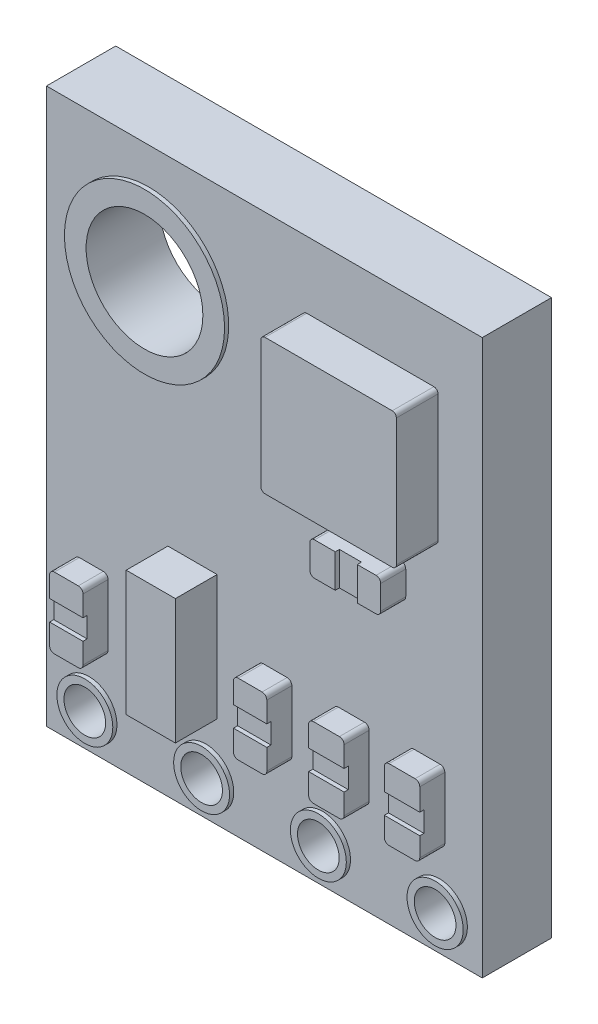
SolidWorks part; units mm, degrees
ref_plane "Alzado" through (0, 0, 0) normal (0, 0, 1) x (1, 0, 0)
ref_plane "Planta" through (0, 0, 0) normal (0, 1, 0) x (1, 0, 0)
ref_plane "Vista lateral" through (0, 0, 0) normal (1, 0, 0) x (0, 0, -1)
sketch "Croquis1" plane through (0, 0, 0) normal (0, 0, 1) x (1, 0, 0)
  line L0 (-5.225, 6.65) -> (5.225, 6.65)
  line L1 (5.225, 6.65) -> (5.225, -6.65)
  line L2 (5.225, -6.65) -> (-5.225, -6.65)
  line L3 (-5.225, -6.65) -> (-5.225, 6.65)
  line L4 (-2.775, 5.26) -> (-2.775, 2.46) construction
  line L5 (-4.175, 3.86) -> (-2.5214, 3.86) construction
  circle A0 centre (-2.775, 3.86) radius 1.4
  point P3 (-5.225, 0)
  point P5 (0, -6.65)
  dimension "D5" = 2.8
  dimension "D1" = 13.3
  dimension "D2" = 10.45
  dimension "D3" = 1.05
  dimension "D4" = 1.39
extrude "Saliente-Extruir1" add sketch "Croquis1" along normal blind 1.66
sketch "Croquis2" plane through (0, 0, 1.66) normal (0, 0, 1) x (1, 0, 0)
  line L0 (1.0149, 5.05) -> (4.0649, 5.05)
  line L1 (4.1649, 4.95) -> (4.1649, 1.9)
  line L2 (4.0649, 1.8) -> (1.0149, 1.8)
  line L3 (0.9149, 1.9) -> (0.9149, 4.95)
  line L4 (5.225, 6.65) -> (-5.225, 6.65) construction
  line L5 (1.8027, 1.0381) -> (3.277, 1.0381) construction
  line L6 (3.3899, 0.9253) -> (3.3899, 0.351) construction
  line L7 (3.277, 0.2381) -> (1.8027, 0.2381) construction
  line L8 (1.6899, 0.351) -> (1.6899, 0.9253) construction
  line L9 (-4.437, -2.75) -> (-3.8627, -2.75) construction
  line L10 (-3.7498, -2.8628) -> (-3.7498, -4.3372) construction
  line L11 (-3.8627, -4.45) -> (-4.437, -4.45) construction
  line L12 (-4.5498, -4.3372) -> (-4.5498, -2.8628) construction
  line L13 (-2.3141, -1.45) -> (-1.1341, -1.45) construction
  line L14 (-1.1341, -1.45) -> (-1.1341, -4.45) construction
  line L15 (-1.1341, -4.45) -> (-2.3141, -4.45) construction
  line L16 (-2.3141, -4.45) -> (-2.3141, -1.45) construction
  line L17 (-0.0292, -2.75) -> (0.5451, -2.75) construction
  line L18 (0.6579, -2.8628) -> (0.6579, -4.3372) construction
  line L19 (0.5451, -4.45) -> (-0.0292, -4.45) construction
  line L20 (-0.1421, -4.3372) -> (-0.1421, -2.8628) construction
  line L21 (1.774, -2.75) -> (2.3983, -2.75) construction
  line L22 (2.5112, -2.8628) -> (2.5112, -4.3372) construction
  line L23 (2.3983, -4.45) -> (1.774, -4.45) construction
  line L24 (1.6612, -4.3372) -> (1.6612, -2.8628) construction
  line L26 (3.589, -2.7167) -> (4.2133, -2.7167) construction
  line L27 (4.3261, -2.8296) -> (4.3261, -4.3039) construction
  line L28 (4.2133, -4.4167) -> (3.589, -4.4167) construction
  line L29 (3.4761, -4.3039) -> (3.4761, -2.8296) construction
  arc A0 (1.0149, 1.8) -> (0.9149, 1.9) centre (1.0149, 1.9) cw
  arc A1 (4.1649, 1.9) -> (4.0649, 1.8) centre (4.0649, 1.9) cw
  arc A2 (4.0649, 5.05) -> (4.1649, 4.95) centre (4.0649, 4.95) cw
  arc A3 (1.0149, 5.05) -> (0.9149, 4.95) centre (1.0149, 4.95) ccw
  arc A4 (4.3261, -4.3039) -> (4.2133, -4.4167) centre (4.2133, -4.3039) cw construction
  arc A5 (3.589, -4.4167) -> (3.4761, -4.3039) centre (3.589, -4.3039) cw construction
  arc A6 (4.2133, -2.7167) -> (4.3261, -2.8296) centre (4.2133, -2.8296) cw construction
  arc A7 (3.4761, -2.8296) -> (3.589, -2.7167) centre (3.589, -2.8296) cw construction
  arc A8 (2.3983, -2.75) -> (2.5112, -2.8628) centre (2.3983, -2.8628) cw construction
  arc A9 (2.5112, -4.3372) -> (2.3983, -4.45) centre (2.3983, -4.3372) cw construction
  arc A10 (1.774, -4.45) -> (1.6612, -4.3372) centre (1.774, -4.3372) cw construction
  arc A11 (1.774, -2.75) -> (1.6612, -2.8628) centre (1.774, -2.8628) ccw construction
  arc A12 (0.5451, -2.75) -> (0.6579, -2.8628) centre (0.5451, -2.8628) cw construction
  arc A13 (0.6579, -4.3372) -> (0.5451, -4.45) centre (0.5451, -4.3372) cw construction
  arc A14 (-0.0292, -4.45) -> (-0.1421, -4.3372) centre (-0.0292, -4.3372) cw construction
  arc A15 (-0.0292, -2.75) -> (-0.1421, -2.8628) centre (-0.0292, -2.8628) ccw construction
  arc A16 (3.277, 1.0381) -> (3.3899, 0.9253) centre (3.277, 0.9253) cw construction
  arc A17 (3.3899, 0.351) -> (3.277, 0.2381) centre (3.277, 0.351) cw construction
  arc A18 (1.8027, 0.2381) -> (1.6899, 0.351) centre (1.8027, 0.351) cw construction
  arc A19 (1.8027, 1.0381) -> (1.6899, 0.9253) centre (1.8027, 0.9253) ccw construction
  arc A20 (-4.437, -4.45) -> (-4.5498, -4.3372) centre (-4.437, -4.3372) cw construction
  arc A21 (-3.7498, -4.3372) -> (-3.8627, -4.45) centre (-3.8627, -4.3372) cw construction
  arc A22 (-3.8627, -2.75) -> (-3.7498, -2.8628) centre (-3.8627, -2.8628) cw construction
  arc A23 (-4.437, -2.75) -> (-4.5498, -2.8628) centre (-4.437, -2.8628) ccw construction
  circle A24 centre (-4.2058, -5.774) radius 0.5 construction
  circle A25 centre (-1.4058, -5.774) radius 0.5 construction
  circle A26 centre (1.3942, -5.774) radius 0.5 construction
  circle A27 centre (4.1942, -5.774) radius 0.5 construction
  point P10 (4.1649, 1.8)
  point P13 (4.1649, 5.05)
  point P36 (2.5399, 1.0381)
  point P38 (2.5399, 1.8)
  point P44 (4.3261, -4.4167)
  point P49 (4.3261, -2.7167)
  point P56 (2.5112, -4.45)
  point P59 (1.6612, -4.45)
  point P64 (0.6579, -2.75)
  point P75 (3.3899, 0.2381)
  point P78 (1.6899, 0.2381)
  point P81 (1.6899, 1.0381)
  point P84 (-4.5498, -4.45)
  point P87 (-3.7498, -4.45)
  point P90 (-3.7498, -2.75)
  point P93 (-4.5498, -2.75)
  dimension "D3" = 0.1
  dimension "D12" = 0.1128
  dimension "D14" = 1
  dimension "D1" = 3.25
  dimension "D2" = 4.85
  dimension "D4" = 3
  dimension "D5" = 1.18
  dimension "D6" = 1.7
  dimension "D7" = 0.8
  dimension "D8" = 0.85
  dimension "D9" = 1.7
  dimension "D10" = 0.8
  dimension "D11" = 1.7
  dimension "D13" = 4
extrude "Saliente-Extruir2" add sketch "Croquis2" along normal blind 1
sketch "Croquis3" plane through (0, 0, 1.66) normal (0, 0, 1) x (1, 0, 0)
  line L0 (0.5451, -4.45) -> (-0.0292, -4.45) construction
  line L1 (-4.437, -2.75) -> (-3.8627, -2.75) construction
  line L2 (-3.7498, -2.8628) -> (-3.7498, -4.3372) construction
  line L3 (-3.8627, -4.45) -> (-4.437, -4.45) construction
  line L4 (-4.5498, -4.3372) -> (-4.5498, -2.8628) construction
  line L5 (0.6579, -2.8628) -> (0.6579, -4.3372) construction
  line L6 (-0.1421, -4.3372) -> (-0.1421, -2.8628) construction
  line L7 (-0.0292, -2.75) -> (0.5451, -2.75) construction
  line L8 (0.5451, -4.45) -> (-0.0292, -4.45)
  line L9 (-0.0292, -2.75) -> (0.5451, -2.75)
  line L10 (-0.1421, -4.3372) -> (-0.1421, -2.8628)
  line L11 (0.6579, -2.8628) -> (0.6579, -4.3372)
  line L12 (-4.5498, -4.3372) -> (-4.5498, -2.8628)
  line L13 (-3.8627, -4.45) -> (-4.437, -4.45)
  line L14 (-3.7498, -2.8628) -> (-3.7498, -4.3372)
  line L15 (-4.437, -2.75) -> (-3.8627, -2.75)
  line L16 (3.589, -2.7167) -> (4.2133, -2.7167) construction
  line L17 (4.3261, -2.8296) -> (4.3261, -4.3039) construction
  line L18 (3.4761, -4.3039) -> (3.4761, -2.8296) construction
  line L19 (4.2133, -4.4167) -> (3.589, -4.4167) construction
  line L20 (1.6612, -4.3372) -> (1.6612, -2.8628) construction
  line L21 (1.774, -2.75) -> (2.3983, -2.75) construction
  line L22 (2.5112, -2.8628) -> (2.5112, -4.3372) construction
  line L23 (2.3983, -4.45) -> (1.774, -4.45) construction
  line L24 (3.589, -2.7167) -> (4.2133, -2.7167)
  line L25 (4.3261, -2.8296) -> (4.3261, -4.3039)
  line L26 (3.4761, -4.3039) -> (3.4761, -2.8296)
  line L27 (4.2133, -4.4167) -> (3.589, -4.4167)
  line L28 (1.6612, -4.3372) -> (1.6612, -2.8628)
  line L29 (1.774, -2.75) -> (2.3983, -2.75)
  line L30 (2.5112, -2.8628) -> (2.5112, -4.3372)
  line L31 (2.3983, -4.45) -> (1.774, -4.45)
  line L32 (1.6899, 0.351) -> (1.6899, 0.9253) construction
  line L33 (1.8027, 1.0381) -> (3.277, 1.0381) construction
  line L34 (3.3899, 0.9253) -> (3.3899, 0.351) construction
  line L35 (3.277, 0.2381) -> (1.8027, 0.2381) construction
  line L36 (1.6899, 0.351) -> (1.6899, 0.9253)
  line L37 (1.8027, 1.0381) -> (3.277, 1.0381)
  line L38 (3.3899, 0.9253) -> (3.3899, 0.351)
  line L39 (3.277, 0.2381) -> (1.8027, 0.2381)
  arc A0 (-3.7498, -2.8628) -> (-3.8627, -2.75) centre (-3.8627, -2.8628) ccw construction
  arc A1 (-3.8627, -4.45) -> (-3.7498, -4.3372) centre (-3.8627, -4.3372) ccw construction
  arc A2 (-4.5498, -4.3372) -> (-4.437, -4.45) centre (-4.437, -4.3372) ccw construction
  arc A3 (-4.437, -2.75) -> (-4.5498, -2.8628) centre (-4.437, -2.8628) ccw construction
  arc A4 (-0.1421, -4.3372) -> (-0.0292, -4.45) centre (-0.0292, -4.3372) ccw construction
  arc A5 (0.6579, -2.8628) -> (0.5451, -2.75) centre (0.5451, -2.8628) ccw construction
  arc A6 (-0.0292, -2.75) -> (-0.1421, -2.8628) centre (-0.0292, -2.8628) ccw construction
  arc A7 (0.5451, -4.45) -> (0.6579, -4.3372) centre (0.5451, -4.3372) ccw construction
  arc A8 (0.5451, -4.45) -> (0.6579, -4.3372) centre (0.5451, -4.3372) ccw
  arc A9 (-0.0292, -2.75) -> (-0.1421, -2.8628) centre (-0.0292, -2.8628) ccw
  arc A10 (0.6579, -2.8628) -> (0.5451, -2.75) centre (0.5451, -2.8628) ccw
  arc A11 (-0.1421, -4.3372) -> (-0.0292, -4.45) centre (-0.0292, -4.3372) ccw
  arc A12 (-4.437, -2.75) -> (-4.5498, -2.8628) centre (-4.437, -2.8628) ccw
  arc A13 (-4.5498, -4.3372) -> (-4.437, -4.45) centre (-4.437, -4.3372) ccw
  arc A14 (-3.8627, -4.45) -> (-3.7498, -4.3372) centre (-3.8627, -4.3372) ccw
  arc A15 (-3.7498, -2.8628) -> (-3.8627, -2.75) centre (-3.8627, -2.8628) ccw
  arc A16 (3.589, -2.7167) -> (3.4761, -2.8296) centre (3.589, -2.8296) ccw construction
  arc A17 (4.3261, -2.8296) -> (4.2133, -2.7167) centre (4.2133, -2.8296) ccw construction
  arc A18 (4.2133, -4.4167) -> (4.3261, -4.3039) centre (4.2133, -4.3039) ccw construction
  arc A19 (3.4761, -4.3039) -> (3.589, -4.4167) centre (3.589, -4.3039) ccw construction
  arc A20 (1.6612, -4.3372) -> (1.774, -4.45) centre (1.774, -4.3372) ccw construction
  arc A21 (1.774, -2.75) -> (1.6612, -2.8628) centre (1.774, -2.8628) ccw construction
  arc A22 (2.5112, -2.8628) -> (2.3983, -2.75) centre (2.3983, -2.8628) ccw construction
  arc A23 (2.3983, -4.45) -> (2.5112, -4.3372) centre (2.3983, -4.3372) ccw construction
  arc A24 (3.589, -2.7167) -> (3.4761, -2.8296) centre (3.589, -2.8296) ccw
  arc A25 (4.3261, -2.8296) -> (4.2133, -2.7167) centre (4.2133, -2.8296) ccw
  arc A26 (4.2133, -4.4167) -> (4.3261, -4.3039) centre (4.2133, -4.3039) ccw
  arc A27 (3.4761, -4.3039) -> (3.589, -4.4167) centre (3.589, -4.3039) ccw
  arc A28 (1.6612, -4.3372) -> (1.774, -4.45) centre (1.774, -4.3372) ccw
  arc A29 (1.774, -2.75) -> (1.6612, -2.8628) centre (1.774, -2.8628) ccw
  arc A30 (2.5112, -2.8628) -> (2.3983, -2.75) centre (2.3983, -2.8628) ccw
  arc A31 (2.3983, -4.45) -> (2.5112, -4.3372) centre (2.3983, -4.3372) ccw
  arc A32 (1.6899, 0.351) -> (1.8027, 0.2381) centre (1.8027, 0.351) ccw construction
  arc A33 (1.8027, 1.0381) -> (1.6899, 0.9253) centre (1.8027, 0.9253) ccw construction
  arc A34 (3.3899, 0.9253) -> (3.277, 1.0381) centre (3.277, 0.9253) ccw construction
  arc A35 (3.277, 0.2381) -> (3.3899, 0.351) centre (3.277, 0.351) ccw construction
  arc A36 (1.6899, 0.351) -> (1.8027, 0.2381) centre (1.8027, 0.351) ccw
  arc A37 (1.8027, 1.0381) -> (1.6899, 0.9253) centre (1.8027, 0.9253) ccw
  arc A38 (3.3899, 0.9253) -> (3.277, 1.0381) centre (3.277, 0.9253) ccw
  arc A39 (3.277, 0.2381) -> (3.3899, 0.351) centre (3.277, 0.351) ccw
extrude "Saliente-Extruir3" add sketch "Croquis3" along normal blind 0.6
sketch "Croquis4" plane through (0, 0, 1.66) normal (0, 0, 1) x (1, 0, 0)
  circle A0 centre (4.1942, -5.774) radius 0.5 construction
  circle A1 centre (1.3942, -5.774) radius 0.5 construction
  circle A2 centre (-1.4058, -5.774) radius 0.5 construction
  circle A3 centre (-4.2058, -5.774) radius 0.5 construction
  circle A4 centre (4.1942, -5.774) radius 0.5
  circle A5 centre (1.3942, -5.774) radius 0.5
  circle A6 centre (-1.4058, -5.774) radius 0.5
  circle A7 centre (-4.2058, -5.774) radius 0.5
extrude "Cortar-Extruir1" cut sketch "Croquis4" against normal blind 2
sketch "Croquis5" plane through (0, 0, 1.66) normal (0, 0, 1) x (1, 0, 0)
  line L0 (-2.3141, -1.45) -> (-1.1341, -1.45) construction
  line L1 (-2.3141, -4.45) -> (-2.3141, -1.45) construction
  line L2 (-1.1341, -1.45) -> (-1.1341, -4.45) construction
  line L3 (-1.1341, -4.45) -> (-2.3141, -4.45) construction
  line L4 (-2.3141, -1.45) -> (-1.1341, -1.45)
  line L5 (-2.3141, -4.45) -> (-2.3141, -1.45)
  line L6 (-1.1341, -1.45) -> (-1.1341, -4.45)
  line L7 (-1.1341, -4.45) -> (-2.3141, -4.45)
extrude "Saliente-Extruir4" add sketch "Croquis5" along normal blind 1
sketch "Croquis6" plane through (0, 0, 1.66) normal (0, 0, 1) x (1, 0, 0)
  circle A0 centre (-4.2058, -5.774) radius 0.6705
  circle A1 centre (-1.4058, -5.774) radius 0.6705
  circle A2 centre (1.3942, -5.774) radius 0.6705
  circle A3 centre (4.1942, -5.774) radius 0.6732
  circle A4 centre (-2.775, 3.86) radius 1.9201
  circle A5 centre (4.1942, -5.774) radius 0.5 construction
  circle A6 centre (1.3942, -5.774) radius 0.5 construction
  circle A7 centre (-1.4058, -5.774) radius 0.5 construction
  circle A8 centre (-4.2058, -5.774) radius 0.5 construction
  circle A9 centre (-2.775, 3.86) radius 1.4 construction
  circle A10 centre (4.1942, -5.774) radius 0.5
  circle A11 centre (1.3942, -5.774) radius 0.5
  circle A12 centre (-1.4058, -5.774) radius 0.5
  circle A13 centre (-4.2058, -5.774) radius 0.5
  circle A14 centre (-2.775, 3.86) radius 1.4
extrude "Saliente-Extruir5" add sketch "Croquis6" along normal blind 0.1
sketch "Croquis7" plane through (0, 0, 2.26) normal (0, 0, 1) x (1, 0, 0)
  line L2 (-4.5498, -3.845) -> (-3.7498, -3.845)
  line L3 (-4.5498, -4.3372) -> (-4.5498, -2.8628) construction
  line L4 (-3.7498, -2.8628) -> (-3.7498, -4.3372) construction
  line L5 (-3.7498, -3.845) -> (-3.7498, -3.3567)
  line L6 (-3.7498, -3.3567) -> (-4.5498, -3.3567)
  line L7 (-4.5498, -3.3567) -> (-4.5498, -3.845)
  line L8 (-0.1421, -3.845) -> (0.6579, -3.845)
  line L9 (-0.1421, -4.3372) -> (-0.1421, -2.8628) construction
  line L10 (0.6579, -2.8628) -> (0.6579, -4.3372) construction
  line L11 (0.6579, -3.845) -> (0.6579, -3.3567)
  line L12 (0.6579, -3.3567) -> (-0.1421, -3.3567)
  line L13 (-0.1421, -3.3567) -> (-0.1421, -3.845)
  line L14 (1.6612, -3.3567) -> (2.5112, -3.3567)
  line L15 (1.6612, -4.3372) -> (1.6612, -2.8628) construction
  line L16 (2.5112, -2.8628) -> (2.5112, -4.3372) construction
  line L17 (2.5112, -3.3567) -> (2.5112, -3.845)
  line L18 (2.5112, -3.845) -> (1.6612, -3.845)
  line L19 (1.6612, -3.845) -> (1.6612, -3.3567)
  line L20 (3.4761, -3.3567) -> (4.3261, -3.3567)
  line L21 (3.4761, -4.3039) -> (3.4761, -2.8296) construction
  line L22 (4.3261, -2.8296) -> (4.3261, -4.3039) construction
  line L23 (4.3261, -3.3567) -> (4.3261, -3.845)
  line L24 (4.3261, -3.845) -> (3.4761, -3.845)
  line L25 (3.4761, -3.845) -> (3.4761, -3.3567)
  line L26 (2.2989, 1.0381) -> (2.2989, 0.2381)
  line L27 (1.8027, 1.0381) -> (3.277, 1.0381) construction
  line L28 (3.277, 0.2381) -> (1.8027, 0.2381) construction
  line L29 (2.2989, 0.2381) -> (2.8278, 0.2381)
  line L30 (2.8278, 0.2381) -> (2.8278, 1.0381)
  line L31 (2.8278, 1.0381) -> (2.2989, 1.0381)
extrude "Cortar-Extruir2" cut sketch "Croquis7" against normal blind 0.1
sketch "Croquis8" plane through (0, 0, 1.66) normal (0, 0, 1) x (1, 0, 0)
  text T0 "bmp180" font "Century Gothic" height in points 8
